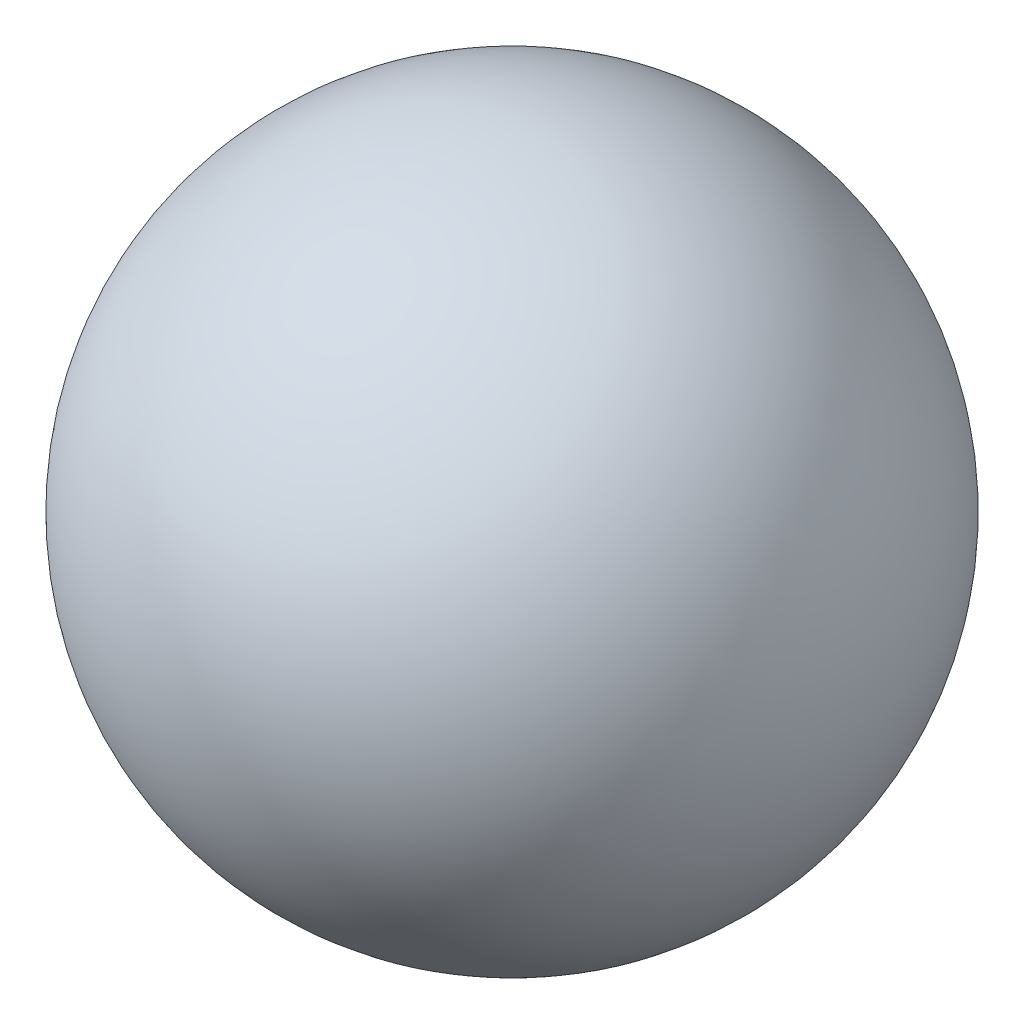
SolidWorks part; units mm, degrees
ref_plane "前视基准面" through (0, 0, 0) normal (0, 0, 1) x (1, 0, 0)
ref_plane "上视基准面" through (0, 0, 0) normal (0, 1, 0) x (1, 0, 0)
ref_plane "右视基准面" through (0, 0, 0) normal (1, 0, 0) x (0, 0, -1)
sketch "草图1" plane through (0, 0, 0) normal (0, 0, 1) x (1, 0, 0)
  line L0 (0, 8.5) -> (0, -8.5)
  arc A0 (0, -8.5) -> (0, 8.5) centre (0, 0) ccw
  dimension "D1" = 17
revolve "旋转1" add sketch "草图1" angle 360 about L0
